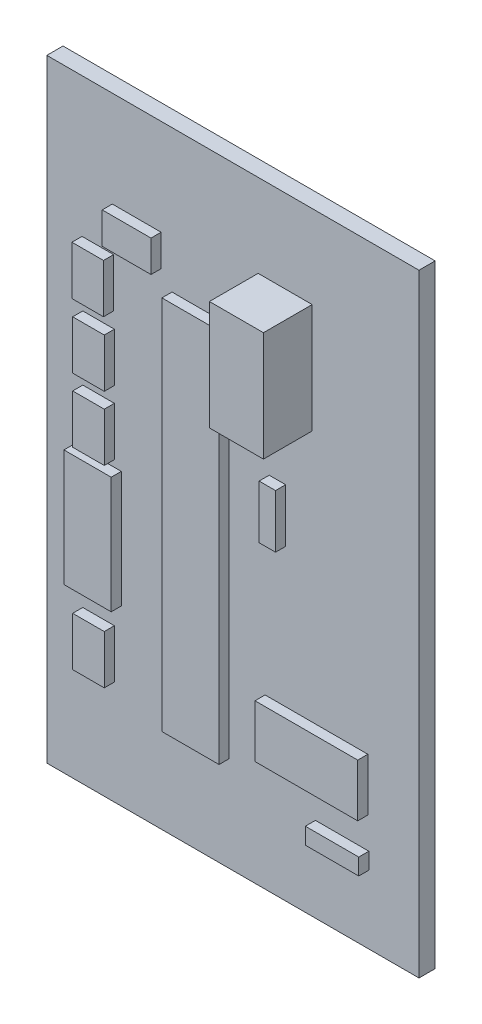
SolidWorks part; units mm, degrees
ref_plane "Front Plane" through (0, 0, 0) normal (0, 0, 1) x (1, 0, 0)
ref_plane "Top Plane" through (0, 0, 0) normal (0, 1, 0) x (1, 0, 0)
ref_plane "Right Plane" through (0, 0, 0) normal (1, 0, 0) x (0, 0, -1)
sketch "Sketch1" plane through (0, 0, 0) normal (0, 0, 1) x (1, 0, 0)
  line L0 (0, 0) -> (36.81, 0)
  line L1 (36.81, 0) -> (36.81, 60.63)
  line L2 (36.81, 60.63) -> (0, 60.63)
  line L3 (0, 60.63) -> (0, 0)
extrude "BOARD" add sketch "Sketch1" along normal blind 1.6 separate body
ref_plane "Plane1" through (0, 0, 1.6) normal (0, 0, 1) x (1, 0, 0)
sketch "Sketch2" plane through (0, 0, 1.6) normal (0, 0, 1) x (1, 0, 0)
  line L0 (6.477, 51.1302) -> (11.303, 51.1302)
  line L1 (11.303, 51.1302) -> (11.303, 48.006)
  line L2 (11.303, 48.006) -> (6.477, 48.006)
  line L3 (6.477, 48.006) -> (6.477, 51.1302)
extrude "C025-030X050-1" add sketch "Sketch2" along normal blind 1 separate body
sketch "Sketch3" plane through (0, 0, 1.6) normal (0, 0, 1) x (1, 0, 0)
  line L0 (3.4798, 42.037) -> (3.4798, 46.863)
  line L1 (3.4798, 46.863) -> (6.604, 46.863)
  line L2 (6.604, 46.863) -> (6.604, 42.037)
  line L3 (6.604, 42.037) -> (3.4798, 42.037)
extrude "C025-030X050-2" add sketch "Sketch3" along normal blind 1 separate body
sketch "Sketch4" plane through (0, 0, 1.6) normal (0, 0, 1) x (1, 0, 0)
  line L0 (6.6802, 40.513) -> (6.6802, 35.687)
  line L1 (6.6802, 35.687) -> (3.556, 35.687)
  line L2 (3.556, 35.687) -> (3.556, 40.513)
  line L3 (3.556, 40.513) -> (6.6802, 40.513)
extrude "C025-030X050-3" add sketch "Sketch4" along normal blind 1 separate body
sketch "Sketch5" plane through (0, 0, 1.6) normal (0, 0, 1) x (1, 0, 0)
  line L0 (6.6802, 34.163) -> (6.6802, 29.337)
  line L1 (6.6802, 29.337) -> (3.556, 29.337)
  line L2 (3.556, 29.337) -> (3.556, 34.163)
  line L3 (3.556, 34.163) -> (6.6802, 34.163)
extrude "C025-030X050-4" add sketch "Sketch5" along normal blind 1 separate body
sketch "Sketch6" plane through (0, 0, 1.6) normal (0, 0, 1) x (1, 0, 0)
  line L0 (6.6802, 15.113) -> (6.6802, 10.287)
  line L1 (6.6802, 10.287) -> (3.556, 10.287)
  line L2 (3.556, 10.287) -> (3.556, 15.113)
  line L3 (3.556, 15.113) -> (6.6802, 15.113)
extrude "C025-030X050-5" add sketch "Sketch6" along normal blind 1 separate body
sketch "Sketch7" plane through (0, 0, 1.6) normal (0, 0, 1) x (1, 0, 0)
  line L0 (31.75, 16.637) -> (31.75, 11.43)
  line L1 (31.75, 11.43) -> (21.59, 11.43)
  line L2 (21.59, 11.43) -> (21.59, 16.637)
  line L3 (21.59, 16.637) -> (31.75, 16.637)
extrude "AB9V-1" add sketch "Sketch7" along normal blind 1 separate body
sketch "Sketch8" plane through (0, 0, 1.6) normal (0, 0, 1) x (1, 0, 0)
  line L0 (12.3825, 46.5455) -> (18.034, 46.5455)
  line L1 (18.034, 46.5455) -> (18.034, 9.398)
  line L2 (18.034, 9.398) -> (12.3825, 9.398)
  line L3 (12.3825, 9.398) -> (12.3825, 46.5455)
extrude "DIL28-1" add sketch "Sketch8" along normal blind 1 separate body
sketch "Sketch9" plane through (0, 0, 0) normal (0, 0, 1) x (1, 0, 0)
  line L0 (31.7735, 35.5835) -> (26.0711, 35.5835)
  line L1 (26.0711, 35.5835) -> (26.0711, 30.1271)
  line L2 (26.0711, 30.1271) -> (31.7735, 30.1271)
  line L3 (31.7735, 30.1271) -> (31.7735, 35.5835)
extrude "RGBLED5050-1" add sketch "Sketch9" against normal blind 1 separate body
sketch "Sketch10" plane through (0, 0, 1.6) normal (0, 0, 1) x (1, 0, 0)
  line L0 (26.245, 52.405) -> (26.245, 41.575)
  line L1 (26.245, 41.575) -> (20.9, 41.575)
  line L2 (20.9, 41.575) -> (20.9, 52.405)
  line L3 (20.9, 52.405) -> (26.245, 52.405)
extrude "TO254P482X997X1968-3P_4.820000-1" add sketch "Sketch10" along normal blind 4.82 separate body
sketch "Sketch11" plane through (0, 0, 1.6) normal (0, 0, 1) x (1, 0, 0)
  line L0 (21.9964, 30.3784) -> (21.9964, 35.6616)
  line L1 (21.9964, 35.6616) -> (23.622, 35.6616)
  line L2 (23.622, 35.6616) -> (23.622, 30.3784)
  line L3 (23.622, 30.3784) -> (21.9964, 30.3784)
extrude "AXIAL-0_3-1" add sketch "Sketch11" along normal blind 1 separate body
sketch "Sketch12" plane through (0, 0, 1.6) normal (0, 0, 1) x (1, 0, 0)
  line L0 (31.8516, 6.7564) -> (26.5684, 6.7564)
  line L1 (26.5684, 6.7564) -> (26.5684, 8.382)
  line L2 (26.5684, 8.382) -> (31.8516, 8.382)
  line L3 (31.8516, 8.382) -> (31.8516, 6.7564)
extrude "AXIAL-0_3-2" add sketch "Sketch12" along normal blind 1 separate body
sketch "Sketch13" plane through (0, 0, 0) normal (0, 0, 1) x (1, 0, 0)
  line L0 (31.3055, 42.3545) -> (31.3055, 54.102)
  line L1 (31.3055, 54.102) -> (27.178, 54.102)
  line L2 (27.178, 54.102) -> (27.178, 42.3545)
  line L3 (27.178, 42.3545) -> (31.3055, 42.3545)
extrude "EG1218-1" add sketch "Sketch13" against normal blind 1 separate body
sketch "Sketch14" plane through (0, 0, 0) normal (0, 0, 1) x (1, 0, 0)
  line L0 (33.16, 22.22) -> (25.26, 22.22)
  line L1 (25.26, 22.22) -> (25.26, 18.42)
  line L2 (25.26, 18.42) -> (33.16, 18.42)
  line L3 (33.16, 18.42) -> (33.16, 22.22)
extrude "TACT_PANA-EVQ-1" add sketch "Sketch14" against normal blind 1 separate body
sketch "Sketch15" plane through (0, 0, 1.6) normal (0, 0, 1) x (1, 0, 0)
  line L0 (7.366, 28.6766) -> (7.366, 17.145)
  line L1 (7.366, 17.145) -> (2.6924, 17.145)
  line L2 (2.6924, 17.145) -> (2.6924, 28.6766)
  line L3 (2.6924, 28.6766) -> (7.366, 28.6766)
extrude "HC49US-1" add sketch "Sketch15" along normal blind 1 separate body
